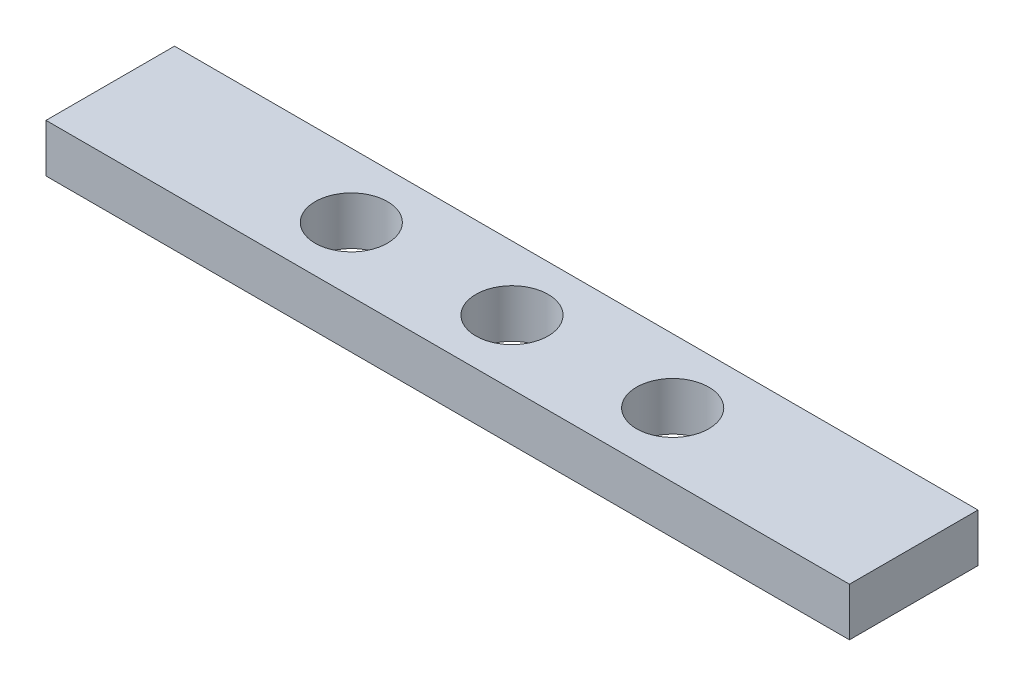
SolidWorks part; units mm, degrees
ref_plane "Front Plane" through (0, 0, 0) normal (0, 0, 1) x (1, 0, 0)
ref_plane "Top Plane" through (0, 0, 0) normal (0, 1, 0) x (1, 0, 0)
ref_plane "Right Plane" through (0, 0, 0) normal (1, 0, 0) x (0, 0, -1)
sketch "Sketch1" plane through (0, 0, 0) normal (0, 1, 0) x (1, 0, 0)
  line L1 (-7.2264, 4.3136) -> (42.7736, 4.3136)
  line L2 (-7.2264, 4.3136) -> (-7.2264, -3.6864)
  line L3 (-7.2264, -3.6864) -> (42.7736, -3.6864)
  line L4 (42.7736, 4.3136) -> (42.7736, -3.6864)
  dimension "D1" = 8
  dimension "D2" = 50
extrude "Boss-Extrude1" add sketch "Sketch1" along normal blind 3
hole_wizard "#8 Clearance Hole1" positions "3DSketch1" profile "Sketch2" hole size "#8" standard "ANSI Inch"
sketch3d "3DSketch1"
  line L0 (-7.2264, 3, -4.3136) -> (-7.2264, 3, 3.6864) construction
  line L1 (42.7736, 3, 3.6864) -> (42.7736, 3, -4.3136) construction
  line L2 (-7.2264, 3, 3.6864) -> (42.7736, 3, 3.6864) construction
  point P0 (7.7736, 3, -0.3136)
  point P2 (27.7736, 3, -0.3136)
  point P12 (17.7736, 3, -0.3136)
  dimension "D1" = 15
  dimension "D2" = 15
  dimension "D3" = 4
  dimension "D4" = 4
  dimension "D5" = 4
  dimension "D6" = 25
sketch "Sketch2" plane through (7.7736, 3, -0.3136) normal (1, 0, 0) x (0, 0, 1)
  line L0 (0, 0) -> (0, 18.3507)
  line L1 (0, 18.3507) -> (2.2479, 17)
  line L2 (2.2479, 17) -> (2.2479, 0)
  line L5 (2.2479, 0) -> (0, 0)
  line L10 (0, 18.3507) -> (-2.2479, 17) construction
  line L11 (0, -6.35) -> (0, 107.95) construction
  dimension "Hole Dia." = 4.4958
  dimension "Hole Depth" = 17
  dimension "Drill Angle" = 118
